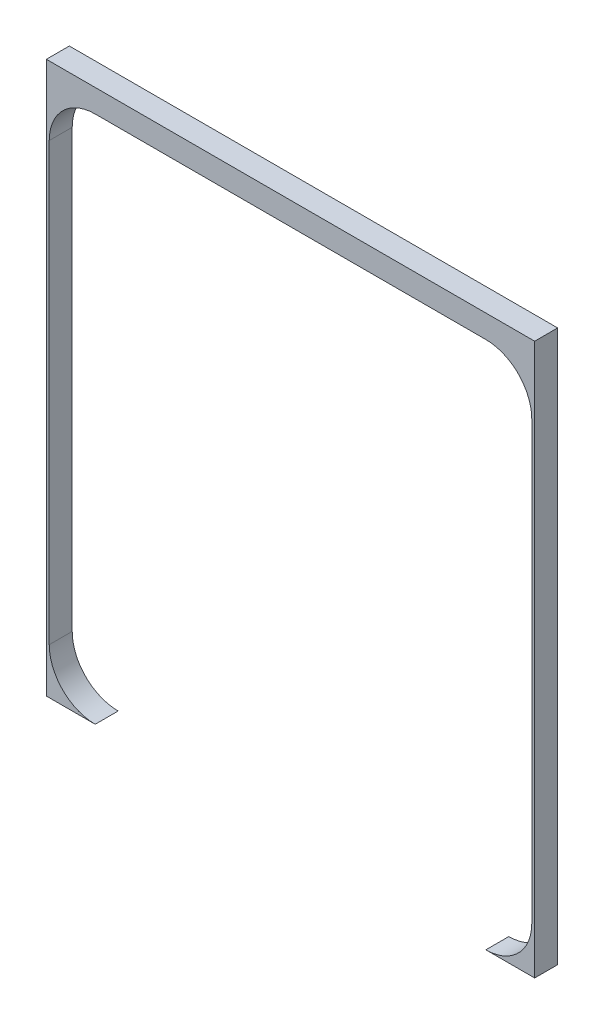
SolidWorks part; units mm, degrees
material "Polyurethane Foam Flexible"
ref_plane "Front Plane" through (0, 0, 0) normal (0, 0, 1) x (1, 0, 0)
ref_plane "Top Plane" through (0, 0, 0) normal (0, 1, 0) x (1, 0, 0)
ref_plane "Right Plane" through (0, 0, 0) normal (1, 0, 0) x (0, 0, -1)
sketch "Sketch1" plane through (0, 0, 0) normal (0, 0, 1) x (1, 0, 0)
  line L1 (-269.875, -304.8) -> (269.875, -304.8)
  line L2 (-269.875, -304.8) -> (-269.875, 304.8)
  line L3 (-269.875, 304.8) -> (269.875, 304.8)
  line L4 (269.875, -304.8) -> (269.875, 304.8)
  line L5 (-269.875, -304.8) -> (269.875, 304.8) construction
  line L6 (-269.875, 304.8) -> (269.875, -304.8) construction
  point P0 (0, 0)
  dimension "D1" = 539.75
  dimension "D2" = 609.6
extrude "Boss-Extrude1" add sketch "Sketch1" along normal blind 25.4
sketch "Sketch2" plane through (0, 0, 0) normal (0, 0, -1) x (-1, 0, 0)
  line L0 (-266.7, -254) -> (-266.7, 228.6) construction
  line L1 (215.9, -304.8) -> (-215.9, -304.8) construction
  line L2 (266.7, 228.6) -> (266.7, -254) construction
  line L3 (-215.9, 279.4) -> (215.9, 279.4) construction
  line L4 (-266.7, -254) -> (-266.7, 228.6)
  line L5 (215.9, -304.8) -> (-215.9, -304.8)
  line L6 (266.7, 228.6) -> (266.7, -254)
  line L7 (-215.9, 279.4) -> (215.9, 279.4)
  arc A0 (-266.7, -254) -> (-215.9, -304.8) centre (-215.9, -254) ccw construction
  arc A1 (215.9, -304.8) -> (266.7, -254) centre (215.9, -254) ccw construction
  arc A2 (266.7, 228.6) -> (215.9, 279.4) centre (215.9, 228.6) ccw construction
  arc A3 (-215.9, 279.4) -> (-266.7, 228.6) centre (-215.9, 228.6) ccw construction
  arc A4 (-266.7, -254) -> (-215.9, -304.8) centre (-215.9, -254) ccw
  arc A5 (215.9, -304.8) -> (266.7, -254) centre (215.9, -254) ccw
  arc A6 (266.7, 228.6) -> (215.9, 279.4) centre (215.9, 228.6) ccw
  arc A7 (-215.9, 279.4) -> (-266.7, 228.6) centre (-215.9, 228.6) ccw
extrude "Cut-Extrude1" cut sketch "Sketch2" against normal through all
